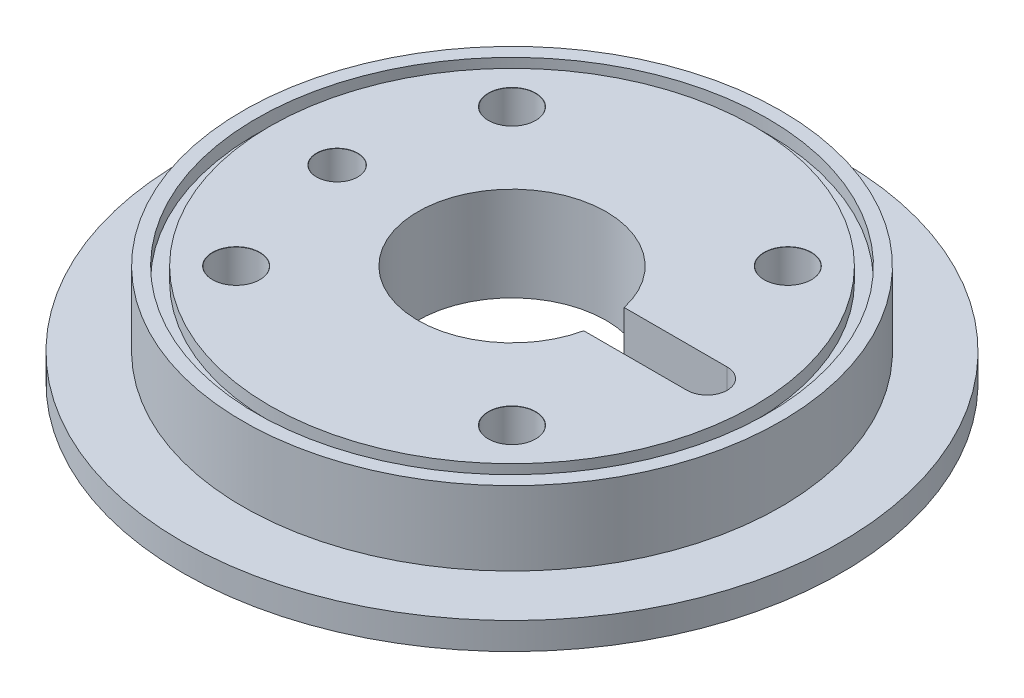
SolidWorks part; units mm, degrees
material "6061-T6 (SS)"
ref_plane "Ebene vorne" through (0, 0, 0) normal (0, 0, 1) x (1, 0, 0)
ref_plane "Ebene oben" through (0, 0, 0) normal (0, 1, 0) x (1, 0, 0)
ref_plane "Ebene rechts" through (0, 0, 0) normal (1, 0, 0) x (0, 0, -1)
sketch "Sketch1" plane through (0, 0, 0) normal (0, 0, 1) x (1, 0, 0)
  line L0 (-14, 1) -> (-14, 15)
  line L6 (0, 0) -> (0, 14.3705) construction
  line L7 (-49, 0) -> (-47, 0)
  line L8 (-47, 0) -> (-47, 2)
  line L9 (-47, 2) -> (-45, 2)
  line L10 (-45, 2) -> (-45, 0)
  line L12 (-45, 0) -> (-43, 0)
  line L13 (-43, 0) -> (-43, 1)
  line L14 (-43, 1) -> (-14, 1)
  line L15 (-40, 15) -> (-38, 15)
  line L16 (-38, 15) -> (-38, 13)
  line L17 (-38, 13) -> (-36, 13)
  line L18 (-36, 13) -> (-36, 15)
  line L19 (-36, 15) -> (-14, 15)
  line L20 (-40, 15) -> (-40, 4)
  line L21 (-40, 4) -> (-49, 4)
  line L22 (-49, 4) -> (-49, 0)
  dimension "D5" = 14
  dimension "D3" = 2
  dimension "D1" = 1
  dimension "D4" = 2
  dimension "D6" = 2
  dimension "D7" = 2
  dimension "D8" = 2
  dimension "D9" = 2
  dimension "D10" = 15
  dimension "D2" = 2
  dimension "D11" = 80
  dimension "D12" = 98
  dimension "D13" = 3
revolve "Revolve1" add sketch "Sketch1" angle 360 about L6
sketch "Sketch2" plane through (0, 15, 0) normal (0, 1, 0) x (1, 0, 0)
  line L0 (0, 0) -> (29, 0) construction
  line L1 (0, 3) -> (29, 3)
  line L2 (0, -3) -> (29, -3)
  arc A0 (0, 3) -> (0, -3) centre (0, 0) ccw
  arc A1 (29, -3) -> (29, 3) centre (29, 0) ccw
  point P3 (14.5, 0)
  dimension "D1" = 3
  dimension "D2" = 29
extrude "Cut-Extrude1" cut sketch "Sketch2" against normal blind 8
hole_wizard "M6 Clearance Hole1" positions "Sketch6" profile "Sketch7" hole size "M6" standard "DIN" end condition up to next
sketch "Sketch6" plane through (0, 15, 0) normal (0, 1, 0) x (1, 0, 0)
  line L0 (0, 0) -> (20.5061, 20.5061) construction
  line L2 (0, 0) -> (20.9263, 0)
  point P0 (20.5061, 20.5061)
  dimension "D1" = 45
  dimension "D2" = 29
sketch "Sketch7" plane through (20.5061, 15, -20.5061) normal (1, 0, 0) x (0, 0, 1)
  line L0 (0, 0) -> (0, 14)
  line L1 (0, 14) -> (3.5, 14)
  line L2 (3.5, 14) -> (3.5, 0.025)
  line L3 (3.5, 0.025) -> (3.525, 0)
  line L5 (3.525, 0) -> (0, 0)
  line L6 (-3.5, 0.025) -> (-3.525, 0) construction
  line L11 (0, -6.35) -> (0, 107.95) construction
  dimension "Thru Hole Dia." = 7
  dimension "Thru Hole Depth" = 14
  dimension "Near C'Sink Dia." = 7.05
  dimension "Near C'Sink Angle" = 90
pattern_circular "CirPattern1" count 4 over 360 about axis through (0, 0, 0) along (0, 1, 0) of "M6 Clearance Hole1"
hole_wizard "Ø6.1 (6.1) Diameter Hole1" positions "Sketch8" profile "Sketch10" hole size "Ø6.1" standard "DIN" end condition up to next
sketch "Sketch8" plane through (0, 15, 0) normal (0, 1, 0) x (1, 0, 0)
  point P0 (-26, 0)
  dimension "D1" = 26
sketch "Sketch10" plane through (-26, 15, 0) normal (1, 0, 0) x (0, 0, 1)
  line L0 (0, 0) -> (0, 14)
  line L1 (0, 14) -> (3.05, 14)
  line L2 (3.05, 14) -> (3.05, 0.025)
  line L3 (3.05, 0.025) -> (3.075, 0)
  line L5 (3.075, 0) -> (0, 0)
  line L6 (-3.05, 0.025) -> (-3.075, 0) construction
  line L11 (0, -6.35) -> (0, 107.95) construction
  dimension "Thru Hole Dia." = 6.1
  dimension "Thru Hole Depth" = 14
  dimension "Near C'Sink Dia." = 6.15
  dimension "Near C'Sink Angle" = 90
equation "\"D8@Sketch1\"=\"D3@Sketch1\""
equation "\"D9@Sketch1\"=\"D4@Sketch1\""
